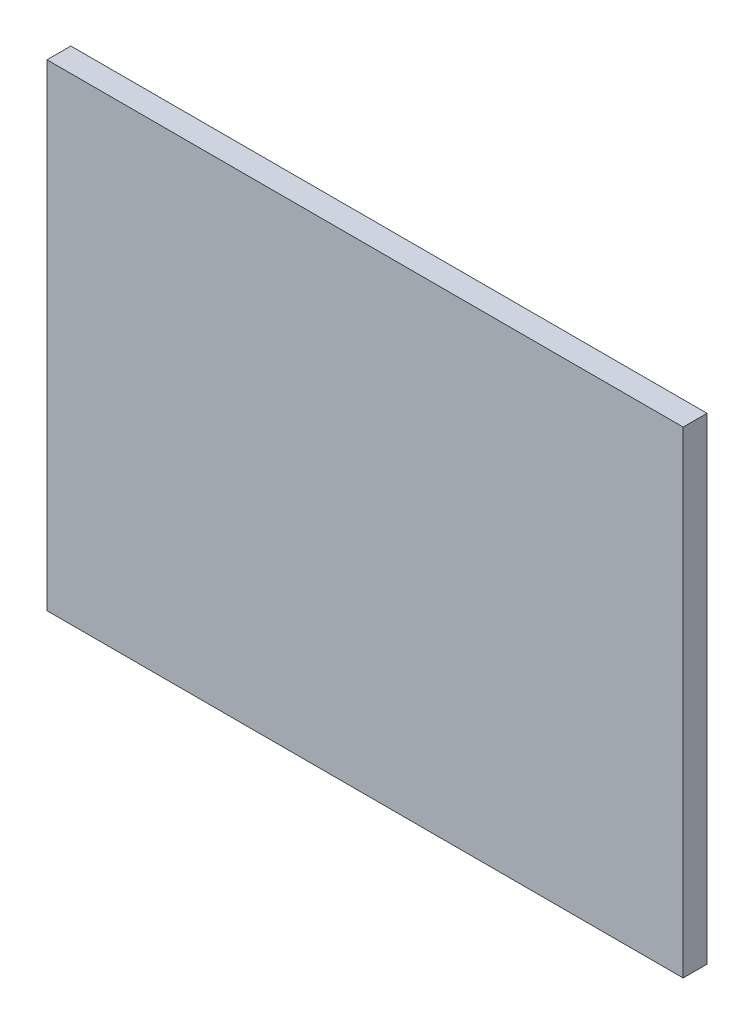
SolidWorks part; units mm, degrees
ref_plane "Front" through (0, 0, 0) normal (0, 0, 1) x (1, 0, 0)
ref_plane "Top" through (0, 0, 0) normal (0, 1, 0) x (1, 0, 0)
ref_plane "Right" through (0, 0, 0) normal (1, 0, 0) x (0, 0, -1)
sketch "Sketch1" plane through (0, 0, 0) normal (0, 0, 1) x (1, 0, 0)
  line L1 (-50.8, -38.1) -> (50.8, -38.1)
  line L2 (-50.8, -38.1) -> (-50.8, 38.1)
  line L3 (-50.8, 38.1) -> (50.8, 38.1)
  line L4 (50.8, -38.1) -> (50.8, 38.1)
  line L5 (-50.8, -38.1) -> (50.8, 38.1) construction
  line L6 (-50.8, 38.1) -> (50.8, -38.1) construction
  point P0 (0, 0)
  dimension "D1" = 101.6
  dimension "D2" = 76.2
extrude "Boss-Extrude1" add sketch "Sketch1" along normal blind 3.81
